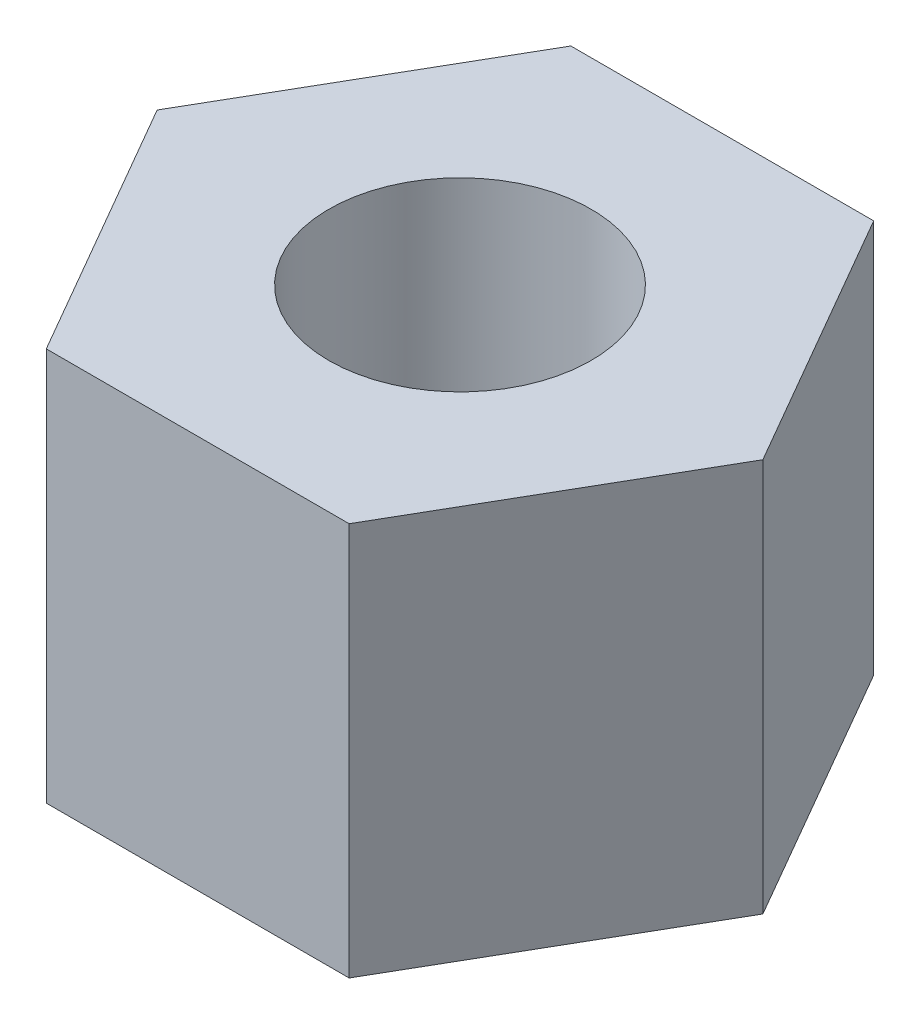
SolidWorks part; units mm, degrees
ref_plane "前视基准面" through (0, 0, 0) normal (0, 0, 1) x (1, 0, 0)
ref_plane "上视基准面" through (0, 0, 0) normal (0, 1, 0) x (1, 0, 0)
ref_plane "右视基准面" through (0, 0, 0) normal (1, 0, 0) x (0, 0, -1)
sketch "草图1" plane through (0, 0, 0) normal (0, 1, 0) x (1, 0, 0)
  line L7 (2.3094, 0) -> (1.1547, 2)
  line L8 (1.1547, 2) -> (-1.1547, 2)
  line L9 (-1.1547, 2) -> (-2.3094, 0)
  line L10 (-2.3094, 0) -> (-1.1547, -2)
  line L11 (-1.1547, -2) -> (1.1547, -2)
  line L12 (1.1547, -2) -> (2.3094, 0)
  circle A0 centre (0, 0) radius 2 construction
  circle A1 centre (0, 0) radius 1
  dimension "D2" = 2
  dimension "D1" = 4
extrude "凸台-拉伸1" add sketch "草图1" along normal blind 3
